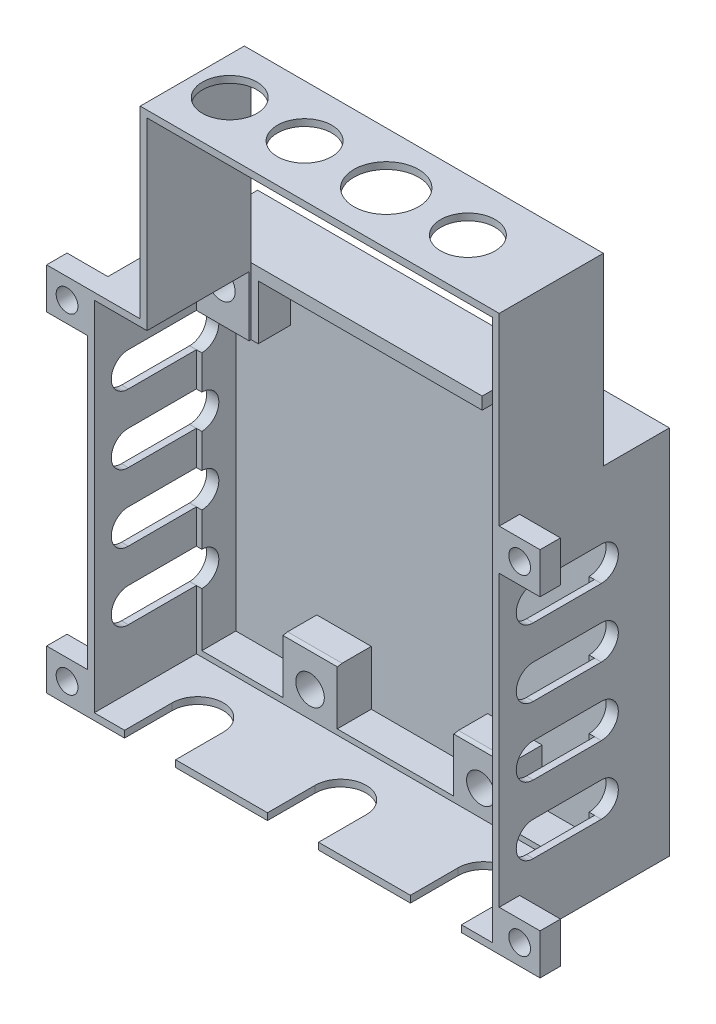
SolidWorks part; units mm, degrees
ref_plane "Alzado" through (0, 0, 0) normal (0, 0, 1) x (1, 0, 0)
ref_plane "Planta" through (0, 0, 0) normal (0, 1, 0) x (1, 0, 0)
ref_plane "Vista lateral" through (0, 0, 0) normal (1, 0, 0) x (0, 0, -1)
sketch "Croquis1" plane through (0, 0, 0) normal (0, 0, 1) x (1, 0, 0)
  line L1 (-73.5556, 30.3447) -> (-13.0556, 30.3447)
  line L2 (-73.5556, 30.3447) -> (-73.5556, -24.1553)
  line L3 (-73.5556, -24.1553) -> (-13.0556, -24.1553)
  line L4 (-13.0556, 30.3447) -> (-13.0556, -24.1553)
  dimension "D1" = 60.5
  dimension "D2" = 54.5
extrude "Saliente-Extruir1" add sketch "Croquis1" along normal blind 25
sketch "Croquis2" plane through (0, 0, 25) normal (0, 0, 1) x (1, 0, 0)
  line L0 (-13.0556, 30.3447) -> (-73.5556, 30.3447) construction
  line L1 (-71.7556, 28.5447) -> (-14.8556, 28.5447)
  line L2 (-71.7556, 28.5447) -> (-71.7556, -22.3553)
  line L3 (-71.7556, -22.3553) -> (-14.8556, -22.3553)
  line L4 (-14.8556, 28.5447) -> (-14.8556, -22.3553)
  line L5 (-13.0556, -24.1553) -> (-13.0556, 30.3447) construction
  line L6 (-73.5556, 30.3447) -> (-73.5556, -24.1553) construction
  line L7 (-73.5556, -24.1553) -> (-13.0556, -24.1553) construction
  dimension "D1" = 1.8
  dimension "D2" = 1.8
  dimension "D3" = 1.8
  dimension "D4" = 1.8
extrude "Cortar-Extruir1" cut sketch "Croquis2" against normal blind 15
sketch "Croquis3" plane through (0, 0, 10) normal (0, 0, 1) x (1, 0, 0)
  line L0 (-14.8556, 28.5447) -> (-71.7556, 28.5447) construction
  line L1 (-71.7556, 28.5447) -> (-71.7556, -22.3553) construction
  line L2 (-43.3056, 28.5447) -> (-43.3056, -22.3553) construction
  line L3 (-71.7556, -22.3553) -> (-14.8556, -22.3553) construction
  line L4 (-71.7556, 20.5447) -> (-71.7556, -22.3553)
  line L5 (-71.7556, 28.5447) -> (-63.7556, 28.5447) construction
  line L6 (-71.7556, 28.5447) -> (-71.7556, 20.5447) construction
  line L7 (-71.7556, 20.5447) -> (-63.7556, 20.5447)
  line L8 (-63.7556, 28.5447) -> (-63.7556, 20.5447)
  line L9 (-59.8556, -22.3553) -> (-51.8556, -22.3553) construction
  line L10 (-59.8556, -22.3553) -> (-59.8556, -14.3553)
  line L11 (-59.8556, -14.3553) -> (-51.8556, -14.3553)
  line L12 (-51.8556, -22.3553) -> (-51.8556, -14.3553)
  line L13 (-71.7556, -22.3553) -> (-59.8556, -22.3553)
  line L14 (-51.8556, -22.3553) -> (-34.7556, -22.3553)
  line L15 (-63.7556, 28.5447) -> (-22.8556, 28.5447)
  line L16 (-34.7556, -22.3553) -> (-34.7556, -14.3553)
  line L17 (-26.7556, -14.3553) -> (-34.7556, -14.3553)
  line L18 (-26.7556, -22.3553) -> (-26.7556, -14.3553)
  line L19 (-14.8556, -22.3553) -> (-26.7556, -22.3553)
  line L20 (-14.8556, 20.5447) -> (-14.8556, -22.3553)
  line L21 (-14.8556, 20.5447) -> (-22.8556, 20.5447)
  line L22 (-22.8556, 28.5447) -> (-22.8556, 20.5447)
  circle A0 centre (-68.9556, 25.7447) radius 2.1
  circle A1 centre (-55.8556, -19.3553) radius 2.1
  circle A2 centre (-30.7556, -19.3553) radius 2.1
  circle A3 centre (-17.6556, 25.7447) radius 2.1
  point P21 (-55.8556, -14.3553)
  dimension "D1" = 4.2
  dimension "D3" = 2.8
  dimension "D4" = 4.2
  dimension "D5" = 3
  dimension "D6" = 15.9
  dimension "D2" = 2.8
  dimension "D7" = 8
  dimension "D8" = 8
  dimension "D9" = 8
  dimension "D10" = 8
extrude "Cortar-Extruir2" cut sketch "Croquis3" against normal blind 5
sketch "Croquis5" plane through (0, -22.3553, 0) normal (0, 1, 0) x (1, 0, 0)
  line L0 (-34.7556, -10) -> (-26.7556, -10) construction
  line L1 (-14.8556, -5) -> (-14.8556, -25) construction
  line L2 (-18.6056, -18) -> (-18.6056, -25)
  line L3 (-71.7556, -25) -> (-14.8556, -25) construction
  line L4 (-18.6056, -25) -> (-26.1056, -25)
  line L5 (-26.1056, -25) -> (-26.1056, -18)
  line L6 (-39.6056, -18) -> (-39.6056, -25)
  line L7 (-39.6056, -25) -> (-47.1056, -25)
  line L8 (-47.1056, -25) -> (-47.1056, -18)
  line L9 (-60.6056, -18) -> (-60.6056, -25)
  line L10 (-60.6056, -25) -> (-68.1056, -25)
  line L11 (-68.1056, -25) -> (-68.1056, -18)
  arc A0 (-18.6056, -18) -> (-26.1056, -18) centre (-22.3556, -18) ccw
  arc A3 (-39.6056, -18) -> (-47.1056, -18) centre (-43.3556, -18) ccw
  arc A4 (-60.6056, -18) -> (-68.1056, -18) centre (-64.3556, -18) ccw
  dimension "D1" = 7.5
  dimension "D2" = 8
  dimension "D3" = 7.5
  dimension "D4" = 3
extrude "Cortar-Extruir3" cut sketch "Croquis5" against normal blind 5
sketch "Croquis6" plane through (0, 28.5447, 0) normal (0, -1, 0) x (1, 0, 0)
  line L0 (-14.8556, 10) -> (-22.8556, 10) construction
  line L1 (-64.8056, 17) -> (-21.8056, 17)
  line L2 (-64.8056, 17) -> (-64.8056, 10)
  line L3 (-64.8056, 10) -> (-30.8556, 10)
  line L4 (-21.8056, 17) -> (-21.8056, 10)
  line L5 (-14.8556, 25) -> (-71.7556, 25) construction
  line L6 (-63.7556, 10) -> (-71.7556, 10) construction
  line L8 (-22.8556, 5) -> (-63.7556, 5) construction
  line L10 (-22.8556, 10) -> (-22.8556, 5)
  line L11 (-22.8556, 5) -> (-30.8556, 5)
  line L12 (-30.8556, 10) -> (-30.8556, 5)
  line L13 (-22.8556, 10) -> (-21.8056, 10)
  point P6 (-43.3056, 17)
  point P9 (-43.3056, 25)
  dimension "D1" = 7
  dimension "D2" = 43
  dimension "D3" = 8
extrude "Cortar-Extruir4" cut sketch "Croquis6" against normal up to vertex (1.8 mm away)
sketch "Croquis9" plane through (-71.7556, 0, 0) normal (1, 0, 0) x (0, 0, -1)
  line L0 (-5, 20.5447) -> (-10, 20.5447) construction
  line L1 (-10, 20.5447) -> (-20, 20.5447)
  line L3 (-10, 15.5447) -> (-20, 15.5447)
  line L7 (-5, 20.5447) -> (-5, -22.3553) construction
  line L8 (-25, 28.5447) -> (-25, -22.3553) construction
  line L9 (-10, 10.5447) -> (-20, 10.5447)
  line L10 (-10, 5.5447) -> (-20, 5.5447)
  line L11 (-10, 0.5447) -> (-20, 0.5447)
  line L12 (-10, -4.4553) -> (-20, -4.4553)
  line L13 (-10, -9.4553) -> (-20, -9.4553)
  line L14 (-10, -14.4553) -> (-20, -14.4553)
  arc A0 (-20, 20.5447) -> (-20, 15.5447) centre (-20, 18.0447) ccw
  arc A1 (-10, 15.5447) -> (-10, 20.5447) centre (-10, 18.0447) ccw
  arc A2 (-20, 10.5447) -> (-20, 5.5447) centre (-20, 8.0447) ccw
  arc A3 (-10, 5.5447) -> (-10, 10.5447) centre (-10, 8.0447) ccw
  arc A4 (-20, 0.5447) -> (-20, -4.4553) centre (-20, -1.9553) ccw
  arc A5 (-10, -4.4553) -> (-10, 0.5447) centre (-10, -1.9553) ccw
  arc A6 (-20, -9.4553) -> (-20, -14.4553) centre (-20, -11.9553) ccw
  arc A7 (-10, -14.4553) -> (-10, -9.4553) centre (-10, -11.9553) ccw
  dimension "D1" = 5
  dimension "D2" = 5
  dimension "D3" = 5
  dimension "D4" = 4
extrude "Cortar-Extruir6" cut sketch "Croquis9" against normal up to vertex and the other way up to surface
sketch "Croquis10" plane through (0, 0, 25) normal (0, 0, 1) x (1, 0, 0)
  line L0 (-43.3056, 30.3447) -> (-43.3056, -24.1553) construction
  line L1 (-73.5556, 30.3447) -> (-79.5556, 30.3447)
  line L2 (-73.5556, 30.3447) -> (-73.5556, 24.3447)
  line L3 (-73.5556, 24.3447) -> (-79.5556, 24.3447)
  line L4 (-79.5556, 30.3447) -> (-79.5556, 24.3447)
  line L5 (-13.0556, 30.3447) -> (-73.5556, 30.3447) construction
  line L6 (-7.0556, 30.3447) -> (-7.0556, 24.3447)
  line L7 (-13.0556, 24.3447) -> (-7.0556, 24.3447)
  line L8 (-13.0556, 30.3447) -> (-13.0556, 24.3447)
  line L9 (-13.0556, 30.3447) -> (-7.0556, 30.3447)
  line L10 (-73.5556, 3.0947) -> (-13.0556, 3.0947) construction
  line L11 (-73.5556, 30.3447) -> (-73.5556, -24.1553) construction
  line L12 (-13.0556, -24.1553) -> (-13.0556, 30.3447) construction
  line L13 (-13.0556, -24.1553) -> (-7.0556, -24.1553)
  line L14 (-13.0556, -24.1553) -> (-13.0556, -18.1553)
  line L15 (-13.0556, -18.1553) -> (-7.0556, -18.1553)
  line L16 (-7.0556, -24.1553) -> (-7.0556, -18.1553)
  line L17 (-79.5556, -24.1553) -> (-79.5556, -18.1553)
  line L18 (-73.5556, -18.1553) -> (-79.5556, -18.1553)
  line L19 (-73.5556, -24.1553) -> (-73.5556, -18.1553)
  line L20 (-73.5556, -24.1553) -> (-79.5556, -24.1553)
  circle A0 centre (-76.5556, 27.3447) radius 1.6
  circle A1 centre (-10.0556, 27.3447) radius 1.6
  circle A2 centre (-10.0556, -21.1553) radius 1.6
  circle A3 centre (-76.5556, -21.1553) radius 1.6
  dimension "D1" = 6
  dimension "D2" = 6
extrude "Saliente-Extruir2" add sketch "Croquis10" against normal blind 3
sketch "Croquis11" plane through (0, 0, 25) normal (0, 0, 1) x (1, 0, 0)
  line L10 (-14.8556, 28.5447) -> (-71.7556, 28.5447) construction
  line L11 (-72.5556, 29.3447) -> (-14.0556, 29.3447)
  line L12 (-72.5556, 29.3447) -> (-72.5556, -23.1553)
  line L13 (-72.5556, -23.1553) -> (-14.0556, -23.1553)
  line L14 (-14.0556, 29.3447) -> (-14.0556, -23.1553)
  line L15 (-71.7556, 28.5447) -> (-71.7556, -22.3553) construction
  line L16 (-14.8556, -22.3553) -> (-14.8556, 28.5447) construction
  line L17 (-18.6056, -22.3553) -> (-14.8556, -22.3553) construction
  dimension "D1" = 0.8
  dimension "D2" = 0.8
  dimension "D3" = 0.8
  dimension "D4" = 0.8
extrude "Cortar-Extruir7" cut sketch "Croquis11" against normal up to vertex (15 mm away)
sketch "Croquis13" plane through (0, 30.3447, 0) normal (0, 1, 0) x (1, 0, 0)
  line L0 (-30.8556, -5) -> (-22.8556, -5) construction
  line L1 (-30.8556, -10) -> (-64.8056, -10)
  line L2 (-30.8556, -10) -> (-30.8556, -9.7)
  line L3 (-30.8556, -9.7) -> (-64.8056, -9.7)
  line L4 (-64.8056, -10) -> (-64.8056, -9.7)
  dimension "D1" = 4.7
extrude "Cortar-Extruir8" cut sketch "Croquis13" against normal up to vertex
sketch "Croquis14" plane through (0, 0, 25) normal (0, 0, 1) x (1, 0, 0)
  line L1 (-14.0556, 29.3447) -> (-64.8056, 29.3447)
  line L2 (-14.0556, 29.3447) -> (-14.0556, 30.3447)
  line L3 (-14.0556, 30.3447) -> (-64.8056, 30.3447)
  line L4 (-64.8056, 29.3447) -> (-64.8056, 30.3447)
extrude "Cortar-Extruir9" cut sketch "Croquis14" against normal up to vertex
sketch "Croquis16" plane through (0, 0, 25) normal (0, 0, 1) x (1, 0, 0)
  line L0 (-64.8056, 30.3447) -> (-64.8056, 56.4141)
  line L1 (-64.8056, 56.4141) -> (-14.0556, 56.4141)
  line L2 (-14.0556, 56.4141) -> (-14.0556, 30.3447)
  line L3 (-14.0556, 30.3447) -> (-13.0556, 30.3447)
  line L4 (-13.0556, 30.3447) -> (-13.0556, 57.4141)
  line L5 (-13.0556, 57.4141) -> (-65.8056, 57.4141)
  line L6 (-65.8056, 57.4141) -> (-65.8056, 30.3447)
  line L7 (-64.8056, 30.3447) -> (-79.5556, 30.3447) construction
  line L8 (-65.8056, 30.3447) -> (-64.8056, 30.3447)
  dimension "D1" = 1
  dimension "D2" = 1
  dimension "D3" = 26.0695
extrude "Saliente-Extruir3" add sketch "Croquis16" against normal up to vertex (15.3 mm away)
sketch "Croquis17" plane through (0, 57.4141, 0) normal (0, 1, 0) x (1, 0, 0)
  line L0 (-65.8056, -9.7) -> (-65.8056, -25) construction
  circle A0 centre (-60.3056, -17.35) radius 4
  circle A1 centre (-49.3056, -17.35) radius 4
  circle A2 centre (-37.3056, -17.35) radius 4.75
  circle A3 centre (-25.3056, -17.35) radius 4
  circle A4 centre (-37.3056, -17.35) radius 6.5 construction
  circle A5 centre (-49.3056, -17.35) radius 5 construction
  circle A6 centre (-60.3056, -17.35) radius 5 construction
  circle A7 centre (-25.3056, -17.35) radius 5 construction
  dimension "D1" = 5.5
  dimension "D5" = 8
  dimension "D6" = 8
  dimension "D7" = 9.5
  dimension "D8" = 8
  dimension "D2" = 11
  dimension "D3" = 12
  dimension "D4" = 12
extrude "Cortar-Extruir10" cut sketch "Croquis17" against normal up to vertex (1 mm away)
